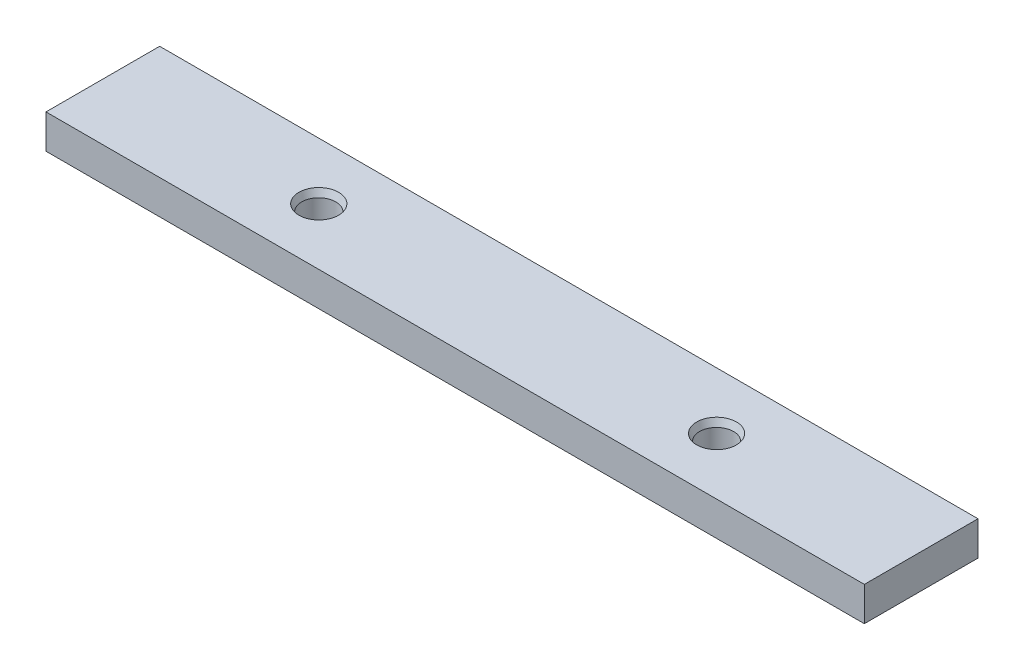
SolidWorks part; units mm, degrees
ref_plane "Front Plane" through (0, 0, 0) normal (0, 0, 1) x (1, 0, 0)
ref_plane "Top Plane" through (0, 0, 0) normal (0, 1, 0) x (1, 0, 0)
ref_plane "Right Plane" through (0, 0, 0) normal (1, 0, 0) x (0, 0, -1)
sketch "Sketch2" plane through (0, 0, 0) normal (0, 1, 0) x (1, 0, 0)
  line L1 (0, 0) -> (144, 0)
  line L2 (0, 0) -> (0, 20)
  line L3 (0, 20) -> (144, 20)
  line L4 (144, 0) -> (144, 20)
  dimension "D1" = 144
  dimension "D2" = 20
extrude "Boss-Extrude1" add sketch "Sketch2" along normal blind 6
hole_wizard "CSK for M2 Flat Head Machine Screw2" positions "Sketch5" profile "Sketch6" countersink size "M2" standard "ANSI Metric" end condition up to next
sketch "Sketch5" plane through (0, 6, 0) normal (0, 1, 0) x (1, 0, 0)
  line L0 (0, 20) -> (0, 0) construction
  line L1 (0, 0) -> (144, 0) construction
  point P0 (38, 10)
  point P2 (108, 10)
  dimension "D1" = 70
  dimension "D2" = 38
  dimension "D3" = 10
  dimension "D4" = 10
sketch "Sketch6" plane through (38, 6, -10) normal (1, 0, 0) x (0, 0, 1)
  line L0 (0, 0) -> (0, 6)
  line L1 (0, 6) -> (3, 6)
  line L2 (3, 6) -> (3, 1.2071)
  line L3 (3, 1.2071) -> (3.5, 0)
  line L5 (3.5, 0) -> (0, 0)
  line L6 (-3, 1.2071) -> (-3.5, 0) construction
  line L11 (0, -6.35) -> (0, 107.95) construction
  dimension "Thru Hole Dia." = 6
  dimension "Thru Hole Depth" = 6
  dimension "Near C'Sink Dia." = 7
  dimension "Near C'Sink Angle" = 45
